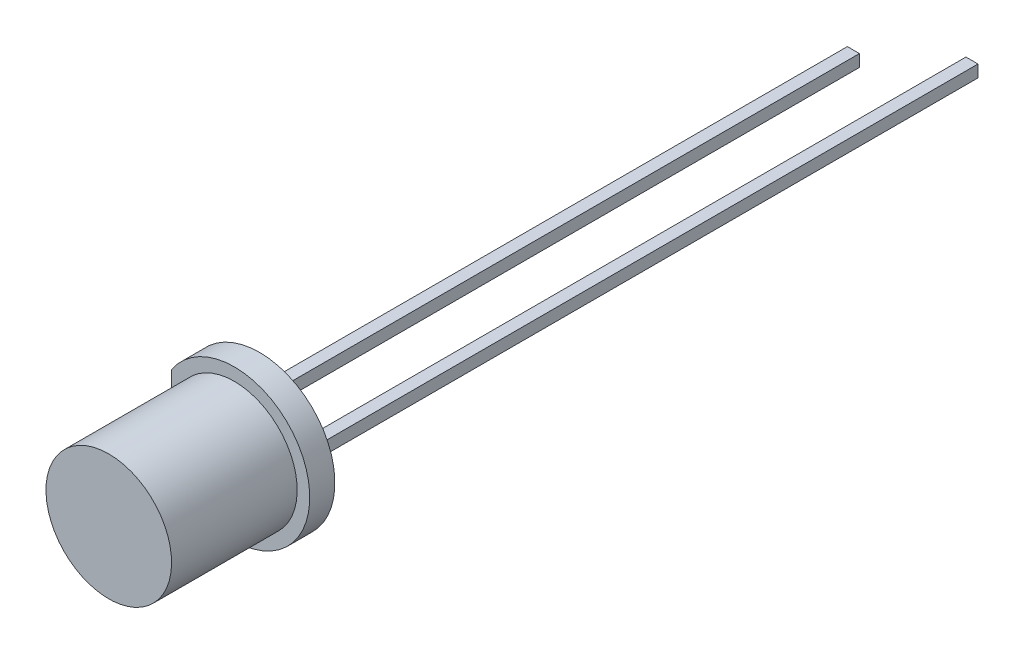
SolidWorks part; units mm, degrees
ref_plane "Plano frontal" through (0, 0, 0) normal (0, 0, 1) x (1, 0, 0)
ref_plane "Plano superior" through (0, 0, 0) normal (0, 1, 0) x (1, 0, 0)
ref_plane "Plano direito" through (0, 0, 0) normal (1, 0, 0) x (0, 0, -1)
sketch "Esboço1" plane through (0, 0, 0) normal (0, 0, 1) x (1, 0, 0)
  circle A0 centre (0, 0) radius 3
  dimension "D1" = 6
extrude "Ressalto-extrusão1" add sketch "Esboço1" along normal blind 1
sketch "Esboço3" plane through (0, 0, 0) normal (1, 0, 0) x (0, 0, -1)
  line L0 (-1, 0) -> (-6, 0)
  line L1 (-1, 3) -> (-1, -3) construction
  line L2 (-6, 2.5) -> (-1, 2.5)
  line L3 (-1, 0) -> (-1, 2.5)
  line L4 (-6, 0) -> (-6, 2.5)
  dimension "D1" = 2.5
  dimension "D2" = 5
revolve "Revolução1" add sketch "Esboço3" angle 360 about L0
sketch "Esboço4" plane through (0, 0, 0) normal (0, 0, -1) x (-1, 0, 0)
  line L0 (2.5, 1.6583) -> (2.5, -1.6583)
  circle A0 centre (0, 0) radius 3 construction
  arc A1 (2.5, -1.6583) -> (2.5, 1.6583) centre (0, 0) ccw
  circle A2 centre (0, 0) radius 2.5 construction
extrude "Corte-extrusão1" cut sketch "Esboço4" against normal up to surface (1 mm away) up to face at (2.5, 0, 1)
sketch "Esboço5" plane through (0, 0, 0) normal (0, 0, -1) x (-1, 0, 0)
  line L0 (-1.12, 0) -> (1.12, 0) construction
  line L1 (-1.6, -0.24) -> (-1.12, -0.24)
  line L2 (-1.6, -0.24) -> (-1.6, 0.24)
  line L3 (-1.6, 0.24) -> (-1.12, 0.24)
  line L4 (-1.12, -0.24) -> (-1.12, 0.24)
  line L5 (1.12, -0.24) -> (1.6, -0.24)
  line L6 (1.12, -0.24) -> (1.12, 0.24)
  line L7 (1.12, 0.24) -> (1.6, 0.24)
  line L8 (1.6, -0.24) -> (1.6, 0.24)
  dimension "D1" = 3.2
  dimension "D2" = 0.48
extrude "Ressalto-extrusão2" add sketch "Esboço5" along normal blind 25 separate body
sketch "Esboço6" plane through (0, 0, -25) normal (0, 0, -1) x (-1, 0, 0)
  line L4 (-1.6, 0.24) -> (-1.6, -0.24)
  line L5 (-1.6, -0.24) -> (-1.12, -0.24)
  line L6 (-1.12, -0.24) -> (-1.12, 0.24)
  line L7 (-1.12, 0.24) -> (-1.6, 0.24)
  line L8 (-1.6, 0.24) -> (-1.6, -0.24)
  line L9 (-1.6, -0.24) -> (-1.12, -0.24)
  line L10 (-1.12, -0.24) -> (-1.12, 0.24)
  line L11 (-1.12, 0.24) -> (-1.6, 0.24)
  dimension "D1" = 0
extrude "Ressalto-extrusão3" add sketch "Esboço6" along normal blind 2 separate body
sketch "Esboço7" plane through (0, 0, 0) normal (0, 1, 0) x (1, 0, 0)
  line L0 (-1.6, 0) -> (-1.6, -3.5)
  line L1 (-1.12, 0) -> (-1.12, -2)
  line L2 (0.02, -2) -> (1.2, -4)
  line L3 (1.2, -4) -> (-1.3, -4)
  line L4 (-1.3, -4) -> (-1.6, -3.5)
  line L5 (-1.12, -2) -> (0.02, -2)
  line L6 (1.6, 0) -> (1.6, -4)
  line L7 (1.6, -4) -> (1.4, -4)
  line L8 (1.4, -4) -> (0.22, -2)
  line L9 (0.22, -2) -> (1.12, -2)
  line L10 (1.12, -2) -> (1.12, 0)
  line L11 (-1.6, 0) -> (-1.12, 0)
  line L12 (1.12, 0) -> (1.6, 0)
  dimension "D1" = 4
  dimension "D2" = 2
  dimension "D3" = 2.8
  dimension "D4" = 0.2
  dimension "D5" = 0.9
  dimension "D6" = 3.5
  dimension "D7" = 2.5
extrude "Corte-extrusão2" cut sketch "Esboço7" against normal mid plane 0.48
sketch "Esboço8" plane through (0, 0, 0) normal (0, 1, 0) x (1, 0, 0)
  line L0 (-1.3, -4) -> (1.2, -4) construction
  line L1 (-1.6, -3.5) -> (-1.3, -4) construction
  line L2 (-1.6, 0) -> (-1.6, -3.5) construction
  line L3 (1.2, -4) -> (0.02, -2) construction
  line L4 (0.02, -2) -> (-1.12, -2) construction
  line L5 (-1.12, -2) -> (-1.12, 0) construction
  line L6 (0.22, -2) -> (1.4, -4) construction
  line L7 (1.12, -2) -> (0.22, -2) construction
  line L8 (1.12, 0) -> (1.12, -2) construction
  line L9 (1.6, -4) -> (1.6, 0) construction
  line L10 (1.4, -4) -> (1.6, -4) construction
  line L11 (-1.12, 0) -> (-1.6, 0) construction
  line L12 (1.6, 0) -> (1.12, 0) construction
  line L13 (-1.3, -4) -> (1.2, -4)
  line L14 (-1.6, -3.5) -> (-1.3, -4)
  line L15 (-1.6, 0) -> (-1.6, -3.5)
  line L16 (1.2, -4) -> (0.02, -2)
  line L17 (0.02, -2) -> (-1.12, -2)
  line L18 (-1.12, -2) -> (-1.12, 0)
  line L19 (0.22, -2) -> (1.4, -4)
  line L20 (1.12, -2) -> (0.22, -2)
  line L21 (1.12, 0) -> (1.12, -2)
  line L22 (1.6, -4) -> (1.6, 0)
  line L23 (1.4, -4) -> (1.6, -4)
  line L24 (-1.12, 0) -> (-1.6, 0)
  line L25 (1.6, 0) -> (1.12, 0)
extrude "Ressalto-extrusão4" add sketch "Esboço8" along normal mid plane 0.48 separate body
combine bodies "Combinar1" operation type add bodies to combine 109 106 104
combine bodies "Combinar2" operation type add bodies to combine 108 105
sketch "Esboço10" plane through (0, 0, 0) normal (0, 1, 0) x (1, 0, 0)
  line L0 (-0.05, -4) -> (-0.05, -3.7)
  line L1 (-1.3, -4) -> (1.2, -4) construction
  line L2 (-0.55, -4) -> (-0.05, -4)
  arc A0 (-0.05, -3.7) -> (-0.55, -4) centre (-0.05, -4.2667) ccw
  dimension "D1" = 0.5
  dimension "D2" = 0.3
revolve "Corte-Revolução1" cut sketch "Esboço10" angle 360 about L0
sketch "Esboço11" plane through (0, 0, 0) normal (0, 1, 0) x (1, 0, 0)
  line L0 (-0.55, -4) -> (-0.05, -4) construction
  line L1 (-0.05, -4) -> (-0.05, -3.7) construction
  line L2 (-0.55, -4) -> (-0.05, -4)
  line L3 (-0.05, -4) -> (-0.05, -3.7)
  arc A0 (-0.05, -3.7) -> (-0.55, -4) centre (-0.05, -4.2667) ccw construction
  arc A1 (-0.05, -3.7) -> (-0.55, -4) centre (-0.05, -4.2667) ccw
revolve "Revolução2" add sketch "Esboço11" angle 360 about L3
combine bodies "Combinar3" operation type add bodies to combine 113 112
sketch "Esboço12" plane through (0, 0, 4) normal (0, 0, 1) x (1, 0, 0)
  circle A0 centre (-0.05, 0) radius 0.2
  arc A1 (0.3886, 0.24) -> (-0.4886, 0.24) centre (-0.05, 0) ccw construction
  dimension "D1" = 0.4
extrude "Corte-extrusão3" cut sketch "Esboço12" against normal blind 0.1
sketch "Esboço13" plane through (0, 0, 0) normal (0, 1, 0) x (1, 0, 0)
  line L0 (1.6, 27) -> (-7.0603, 32)
  line L1 (1.6, 27) -> (1.12, 27) construction
  dimension "D1" = 10
  dimension "D2" = 30
ref_plane "Plano1" through (12.0913, 0, -20.9428) normal (0.5, 0, -0.866) x (-0.866, 0, -0.5)
